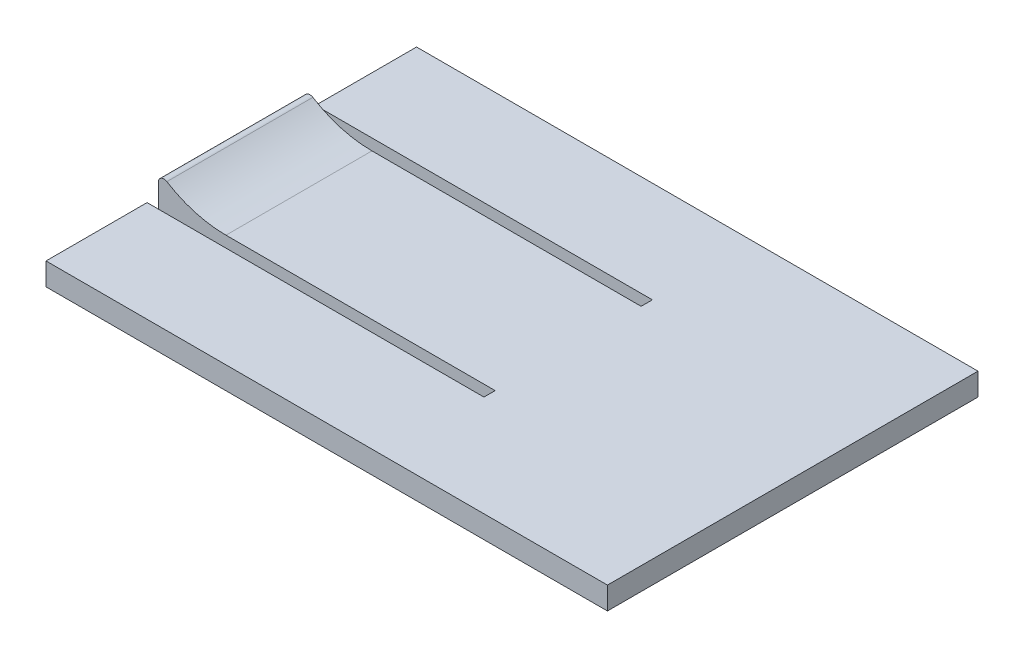
SolidWorks part; units mm, degrees
ref_plane "Front Plane" through (0, 0, 0) normal (0, 0, 1) x (1, 0, 0)
ref_plane "Top Plane" through (0, 0, 0) normal (0, 1, 0) x (1, 0, 0)
ref_plane "Right Plane" through (0, 0, 0) normal (1, 0, 0) x (0, 0, -1)
sketch "Sketch2" plane through (0, 0, 0) normal (1, 0, 0) x (0, 0, -1)
  line L1 (-33, 2) -> (0, 2)
  line L2 (-33, 2) -> (-33, 0)
  line L3 (-33, 0) -> (0, 0)
  line L4 (0, 2) -> (0, 0)
  dimension "D1" = 33
  dimension "D2" = 2
extrude "Boss-Extrude1" add sketch "Sketch2" along normal blind 50
sketch "Sketch3" plane through (0, 2, 0) normal (0, 1, 0) x (1, 0, 0)
  line L0 (0, 0) -> (0, -33) construction
  line L10 (0, -9) -> (0, -10)
  line L13 (0, -24) -> (30, -24)
  line L14 (0, -24) -> (0, -23)
  line L15 (0, -23) -> (30, -23)
  line L16 (30, -24) -> (30, -23)
  line L17 (0, -23) -> (0, -24)
  line L18 (0, -9) -> (30, -9)
  line L19 (0, -9) -> (0, -10)
  line L20 (0, -10) -> (30, -10)
  line L21 (30, -9) -> (30, -10)
  point P9 (0, -16.5)
  line M5 (0, 0) -> (0, -33)
  dimension "D1" = 15
  dimension "D2" = 30
  dimension "D3" = 30
  dimension "D4" = 1
  dimension "D5" = 1
extrude "Cut-Extrude2" cut sketch "Sketch3" against normal blind 50 contours L21 L18 L20 M5 | L13 L16 L15 M5
sketch "Sketch4" plane through (0, 2, 0) normal (0, 1, 0) x (1, 0, 0)
  line L0 (0, -23) -> (30, -23) construction
  line L1 (0, -10) -> (3, -10)
  line L2 (0, -10) -> (0, -23)
  line L3 (0, -23) -> (3, -23)
  line L4 (3, -10) -> (3, -23)
  dimension "D1" = 3
extrude "Boss-Extrude2" add sketch "Sketch4" along normal blind 2
sketch "Sketch5" plane through (0, 0, 23) normal (0, 0, 1) x (1, 0, 0)
  line L0 (3, 2) -> (0, 4)
  line L1 (0, 4) -> (3, 4)
  line L2 (3, 4) -> (3, 2)
extrude "Cut-Extrude3" cut sketch "Sketch5" against normal up to surface (13 mm away) up to face at (11, 2, 10)
fillet "Fillet1" radius 10 1 edges at (3, 2, 16.5)
fillet "Fillet2" radius 0.5 1 edges at (0, 4, 16.5)
